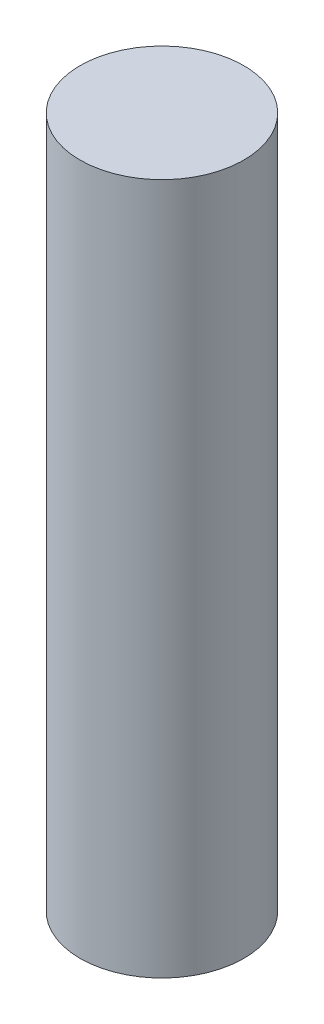
SolidWorks part; units mm, degrees
material "6061-T6 (SS)"
ref_plane "Front Plane" through (0, 0, 0) normal (0, 0, 1) x (1, 0, 0)
ref_plane "Top Plane" through (0, 0, 0) normal (0, 1, 0) x (1, 0, 0)
ref_plane "Right Plane" through (0, 0, 0) normal (1, 0, 0) x (0, 0, -1)
sketch "Sketch1" plane through (0, 0, 0) normal (0, 1, 0) x (1, 0, 0)
  circle A0 centre (0, 0) radius 25.5651
  dimension "D1" = 51.1302
extrude "Boss-Extrude1" add sketch "Sketch1" along normal blind 215.9
